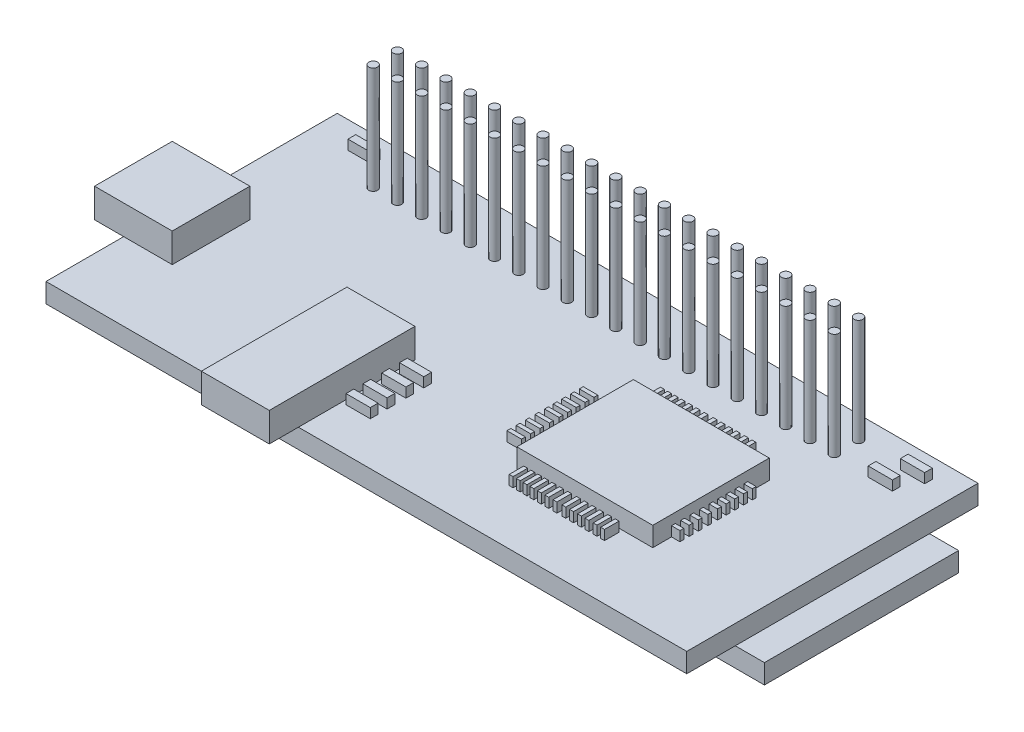
SolidWorks part; units mm, degrees
ref_plane "Front Plane" through (0, 0, 0) normal (0, 0, 1) x (1, 0, 0)
ref_plane "Top Plane" through (0, 0, 0) normal (0, 1, 0) x (1, 0, 0)
ref_plane "Right Plane" through (0, 0, 0) normal (1, 0, 0) x (0, 0, -1)
sketch "Sketch1" plane through (0, 0, 0) normal (0, 1, 0) x (1, 0, 0)
  line L0 (0, 0) -> (66, 0)
  line L1 (66, 0) -> (66, 30)
  line L2 (66, 30) -> (0, 30)
  line L3 (0, 30) -> (0, 0)
  dimension "D1" = 66
  dimension "D2" = 30
extrude "Boss-Extrude1" add sketch "Sketch1" along normal blind 2
sketch "Sketch2" plane through (0, 2, 0) normal (0, 1, 0) x (1, 0, 0)
  line L0 (0, 30) -> (0, 0) construction
  line L1 (66, 30) -> (0, 30) construction
  circle A0 centre (8.5, 27.7) radius 0.45
  circle A1 centre (8.5, 25.2) radius 0.45
  circle A2 centre (11, 27.7) radius 0.45
  circle A3 centre (11, 25.2) radius 0.45
  circle A4 centre (13.5, 27.7) radius 0.45
  circle A5 centre (13.5, 25.2) radius 0.45
  circle A6 centre (16, 27.7) radius 0.45
  circle A7 centre (16, 25.2) radius 0.45
  circle A8 centre (18.5, 27.7) radius 0.45
  circle A9 centre (18.5, 25.2) radius 0.45
  circle A10 centre (21, 27.7) radius 0.45
  circle A11 centre (21, 25.2) radius 0.45
  circle A12 centre (23.5, 27.7) radius 0.45
  circle A13 centre (23.5, 25.2) radius 0.45
  circle A14 centre (26, 27.7) radius 0.45
  circle A15 centre (26, 25.2) radius 0.45
  circle A16 centre (28.5, 27.7) radius 0.45
  circle A17 centre (28.5, 25.2) radius 0.45
  circle A18 centre (31, 27.7) radius 0.45
  circle A19 centre (31, 25.2) radius 0.45
  circle A20 centre (33.5, 27.7) radius 0.45
  circle A21 centre (33.5, 25.2) radius 0.45
  circle A22 centre (36, 27.7) radius 0.45
  circle A23 centre (36, 25.2) radius 0.45
  circle A24 centre (38.5, 27.7) radius 0.45
  circle A25 centre (38.5, 25.2) radius 0.45
  circle A26 centre (41, 27.7) radius 0.45
  circle A27 centre (41, 25.2) radius 0.45
  circle A28 centre (43.5, 27.7) radius 0.45
  circle A29 centre (43.5, 25.2) radius 0.45
  circle A30 centre (46, 27.7) radius 0.45
  circle A31 centre (46, 25.2) radius 0.45
  circle A32 centre (48.5, 27.7) radius 0.45
  circle A33 centre (48.5, 25.2) radius 0.45
  circle A34 centre (51, 27.7) radius 0.45
  circle A35 centre (51, 25.2) radius 0.45
  circle A36 centre (53.5, 27.7) radius 0.45
  circle A37 centre (53.5, 25.2) radius 0.45
  circle A38 centre (56, 27.7) radius 0.45
  circle A39 centre (56, 25.2) radius 0.45
  dimension "D1" = 0.9
  dimension "D6" = 0.9
  dimension "D2" = 8.5
  dimension "D3" = 2.3
  dimension "D4" = 2.5
  dimension "D5" = 8.5
  dimension "D7" = 20
extrude "Boss-Extrude2" add sketch "Sketch2" along normal blind 11
sketch "Sketch3" plane through (0, 2, 0) normal (0, 1, 0) x (1, 0, 0)
  line L0 (60.8, 28) -> (63.3, 28)
  line L1 (63.3, 28) -> (63.3, 27.2)
  line L2 (63.3, 27.2) -> (60.8, 27.2)
  line L3 (60.8, 27.2) -> (60.8, 28)
  line L4 (66, 30) -> (0, 30) construction
  line L5 (66, 0) -> (66, 30) construction
  line L6 (62.3, 24.8879) -> (59.8, 24.8879)
  line L7 (62.3, 25.6879) -> (62.3, 24.8879)
  line L8 (59.8, 25.6879) -> (62.3, 25.6879)
  line L9 (59.8, 24.8879) -> (59.8, 25.6879)
  line L10 (6.3546, 27.25) -> (3.8546, 27.25)
  line L11 (6.3546, 28.05) -> (6.3546, 27.25)
  line L12 (3.8546, 28.05) -> (6.3546, 28.05)
  line L13 (3.8546, 27.25) -> (3.8546, 28.05)
  line L14 (26.45, 9.9597) -> (26.45, 10.7597)
  line L15 (28.95, 10.7597) -> (28.95, 9.9597)
  line L16 (26.45, 10.7597) -> (28.95, 10.7597)
  line L17 (28.95, 9.9597) -> (26.45, 9.9597)
  line L18 (26.45, 8.1238) -> (26.45, 8.9238)
  line L19 (28.95, 8.9238) -> (28.95, 8.1238)
  line L20 (26.45, 8.9238) -> (28.95, 8.9238)
  line L21 (28.95, 8.1238) -> (26.45, 8.1238)
  line L22 (26.45, 6.186) -> (26.45, 6.986)
  line L23 (28.95, 6.986) -> (28.95, 6.186)
  line L24 (26.45, 6.986) -> (28.95, 6.986)
  line L25 (28.95, 6.186) -> (26.45, 6.186)
  line L26 (26.45, 4.4521) -> (26.45, 5.2521)
  line L27 (28.95, 5.2521) -> (28.95, 4.4521)
  line L28 (26.45, 5.2521) -> (28.95, 5.2521)
  line L29 (28.95, 4.4521) -> (26.45, 4.4521)
  dimension "D1" = 0.8
  dimension "D2" = 2.5
  dimension "D3" = 2
  dimension "D4" = 2.7
extrude "Boss-Extrude3" add sketch "Sketch3" along normal blind 1
sketch "Sketch4" plane through (0, 2, 0) normal (0, 1, 0) x (1, 0, 0)
  line L0 (26, 12) -> (26, -3)
  line L2 (26, 12) -> (19, 12)
  line L3 (19, 12) -> (19, -3)
  line L4 (26, -3) -> (19, -3)
  line L6 (0, 30) -> (0, 0) construction
  line L7 (0, 0) -> (66, 0) construction
  dimension "D1" = 19
  dimension "D2" = 7
  dimension "D3" = 3
  dimension "D4" = 15
extrude "Boss-Extrude4" add sketch "Sketch4" along normal blind 3
sketch "Sketch6" plane through (0, 2, 0) normal (0, 1, 0) x (1, 0, 0)
  line L0 (-3, 16) -> (-3, 8)
  line L2 (-3, 8) -> (5, 8)
  line L3 (5, 8) -> (5, 16)
  line L4 (5, 16) -> (-3, 16)
  line L6 (0, 30) -> (0, 0) construction
  line L7 (0, 0) -> (19, 0) construction
  dimension "D1" = 3
  dimension "D2" = 8
  dimension "D3" = 8
  dimension "D4" = 8
extrude "Boss-Extrude6" add sketch "Sketch6" along normal blind 3
sketch "Sketch7" plane through (0, 2, 0) normal (0, 1, 0) x (1, 0, 0)
  line L0 (41, 19.5) -> (55, 19.5)
  line L1 (55, 19.5) -> (55, 7.5)
  line L2 (55, 7.5) -> (41, 7.5)
  line L3 (41, 7.5) -> (41, 19.5)
  line L4 (66, 0) -> (66, 30) construction
  line L5 (26, 0) -> (66, 0) construction
  dimension "D1" = 12
  dimension "D2" = 14
  dimension "D3" = 11
  dimension "D4" = 7.5
extrude "Boss-Extrude7" add sketch "Sketch7" along normal blind 2
sketch "Sketch9" plane through (0, 2, 0) normal (0, 1, 0) x (1, 0, 0)
  line L0 (54.3702, 13.7) -> (54.3702, 13.3)
  line L1 (54.3702, 13.3) -> (55.8702, 13.3)
  line L2 (54.3702, 13.7) -> (55.8702, 13.7)
  line L3 (55.8702, 13.7) -> (55.8702, 13.3)
  line L4 (54.3702, 12.3034) -> (55.8702, 12.3034)
  line L5 (54.3702, 12.7034) -> (54.3702, 12.3034)
  line L6 (55.8702, 12.7034) -> (55.8702, 12.3034)
  line L7 (54.3702, 12.7034) -> (55.8702, 12.7034)
  line L8 (54.3702, 11.3163) -> (55.8702, 11.3163)
  line L9 (54.3702, 11.7163) -> (54.3702, 11.3163)
  line L10 (55.8702, 11.7163) -> (55.8702, 11.3163)
  line L11 (54.3702, 11.7163) -> (55.8702, 11.7163)
  line L12 (54.3702, 10.3707) -> (55.8702, 10.3707)
  line L13 (54.3702, 10.7707) -> (54.3702, 10.3707)
  line L14 (55.8702, 10.7707) -> (55.8702, 10.3707)
  line L15 (54.3702, 10.7707) -> (55.8702, 10.7707)
  line L16 (54.3702, 9.4251) -> (55.8702, 9.4251)
  line L17 (54.3702, 9.8251) -> (54.3702, 9.4251)
  line L18 (55.8702, 9.8251) -> (55.8702, 9.4251)
  line L19 (54.3702, 9.8251) -> (55.8702, 9.8251)
  line L20 (54.3702, 14.1882) -> (55.8702, 14.1882)
  line L21 (54.3702, 14.5882) -> (54.3702, 14.1882)
  line L22 (55.8702, 14.5882) -> (55.8702, 14.1882)
  line L23 (54.3702, 14.5882) -> (55.8702, 14.5882)
  line L24 (54.3702, 15.0637) -> (55.8702, 15.0637)
  line L25 (54.3702, 15.4637) -> (54.3702, 15.0637)
  line L26 (55.8702, 15.4637) -> (55.8702, 15.0637)
  line L27 (54.3702, 15.4637) -> (55.8702, 15.4637)
  line L28 (54.3702, 15.9743) -> (55.8702, 15.9743)
  line L29 (54.3702, 16.3743) -> (54.3702, 15.9743)
  line L30 (55.8702, 16.3743) -> (55.8702, 15.9743)
  line L31 (54.3702, 16.3743) -> (55.8702, 16.3743)
  line L32 (54.3702, 16.8849) -> (55.8702, 16.8849)
  line L33 (54.3702, 17.2849) -> (54.3702, 16.8849)
  line L34 (55.8702, 17.2849) -> (55.8702, 16.8849)
  line L35 (54.3702, 17.2849) -> (55.8702, 17.2849)
  line L36 (39.5528, 12.7034) -> (39.5528, 12.3034)
  line L37 (38.0528, 14.5882) -> (38.0528, 14.1882)
  line L38 (38.0528, 12.3034) -> (39.5528, 12.3034)
  line L39 (38.0528, 11.3163) -> (39.5528, 11.3163)
  line L40 (38.0528, 14.5882) -> (39.5528, 14.5882)
  line L41 (39.5528, 11.7163) -> (39.5528, 11.3163)
  line L42 (38.0528, 15.4637) -> (38.0528, 15.0637)
  line L43 (38.0528, 10.3707) -> (39.5528, 10.3707)
  line L44 (38.0528, 15.4637) -> (39.5528, 15.4637)
  line L45 (39.5528, 10.7707) -> (39.5528, 10.3707)
  line L46 (38.0528, 16.3743) -> (38.0528, 15.9743)
  line L47 (46.5835, 21.2217) -> (46.5835, 19.7217)
  line L48 (38.0528, 13.7) -> (39.5528, 13.7)
  line L49 (38.0528, 9.4251) -> (39.5528, 9.4251)
  line L50 (46.9835, 19.7217) -> (46.5835, 19.7217)
  line L51 (39.5528, 9.8251) -> (39.5528, 9.4251)
  line L52 (39.5528, 13.7) -> (39.5528, 13.3)
  line L53 (38.0528, 12.7034) -> (38.0528, 12.3034)
  line L54 (38.0528, 14.1882) -> (39.5528, 14.1882)
  line L55 (38.0528, 12.7034) -> (39.5528, 12.7034)
  line L56 (39.5528, 14.5882) -> (39.5528, 14.1882)
  line L57 (38.0528, 11.7163) -> (38.0528, 11.3163)
  line L58 (38.0528, 15.0637) -> (39.5528, 15.0637)
  line L59 (38.0528, 11.7163) -> (39.5528, 11.7163)
  line L60 (39.5528, 15.4637) -> (39.5528, 15.0637)
  line L61 (38.0528, 13.3) -> (39.5528, 13.3)
  line L62 (38.0528, 10.7707) -> (38.0528, 10.3707)
  line L63 (38.0528, 15.9743) -> (39.5528, 15.9743)
  line L64 (38.0528, 16.3743) -> (39.5528, 16.3743)
  line L65 (38.0528, 13.7) -> (38.0528, 13.3)
  line L66 (38.0528, 10.7707) -> (39.5528, 10.7707)
  line L67 (39.5528, 16.3743) -> (39.5528, 15.9743)
  line L68 (46.9835, 21.2217) -> (46.5835, 21.2217)
  line L69 (38.0528, 9.8251) -> (38.0528, 9.4251)
  line L70 (46.9835, 21.2217) -> (46.9835, 19.7217)
  line L71 (38.0528, 9.8251) -> (39.5528, 9.8251)
  line L72 (38.0528, 17.2849) -> (38.0528, 16.8849)
  line L73 (38.0528, 16.8849) -> (39.5528, 16.8849)
  line L74 (39.5528, 17.2849) -> (39.5528, 16.8849)
  line L75 (38.0528, 17.2849) -> (39.5528, 17.2849)
  line L76 (47.4941, 21.2217) -> (47.4941, 19.7217)
  line L77 (47.8941, 19.7217) -> (47.4941, 19.7217)
  line L78 (47.8941, 21.2217) -> (47.8941, 19.7217)
  line L79 (47.8941, 21.2217) -> (47.4941, 21.2217)
  line L80 (48.2996, 21.2217) -> (48.2996, 19.7217)
  line L81 (48.6996, 19.7217) -> (48.2996, 19.7217)
  line L82 (48.6996, 21.2217) -> (48.6996, 19.7217)
  line L83 (48.6996, 21.2217) -> (48.2996, 21.2217)
  line L84 (49.1051, 21.2217) -> (49.1051, 19.7217)
  line L85 (49.5051, 19.7217) -> (49.1051, 19.7217)
  line L86 (49.5051, 21.2217) -> (49.5051, 19.7217)
  line L87 (49.5051, 21.2217) -> (49.1051, 21.2217)
  line L88 (49.8756, 21.2217) -> (49.8756, 19.7217)
  line L89 (50.2756, 19.7217) -> (49.8756, 19.7217)
  line L90 (50.2756, 21.2217) -> (50.2756, 19.7217)
  line L91 (50.2756, 21.2217) -> (49.8756, 21.2217)
  line L92 (50.7162, 21.2217) -> (50.7162, 19.7217)
  line L93 (51.1162, 19.7217) -> (50.7162, 19.7217)
  line L94 (51.1162, 21.2217) -> (51.1162, 19.7217)
  line L95 (51.1162, 21.2217) -> (50.7162, 21.2217)
  line L96 (51.4866, 21.2217) -> (51.4866, 19.7217)
  line L97 (51.8866, 19.7217) -> (51.4866, 19.7217)
  line L98 (51.8866, 21.2217) -> (51.8866, 19.7217)
  line L99 (51.8866, 21.2217) -> (51.4866, 21.2217)
  line L100 (45.743, 21.2217) -> (45.743, 19.7217)
  line L101 (46.143, 19.7217) -> (45.743, 19.7217)
  line L102 (46.143, 21.2217) -> (46.143, 19.7217)
  line L103 (46.143, 21.2217) -> (45.743, 21.2217)
  line L104 (44.9725, 21.2217) -> (44.9725, 19.7217)
  line L105 (45.3725, 19.7217) -> (44.9725, 19.7217)
  line L106 (45.3725, 21.2217) -> (45.3725, 19.7217)
  line L107 (45.3725, 21.2217) -> (44.9725, 21.2217)
  line L108 (44.202, 21.2217) -> (44.202, 19.7217)
  line L109 (44.602, 19.7217) -> (44.202, 19.7217)
  line L110 (44.602, 21.2217) -> (44.602, 19.7217)
  line L111 (44.602, 21.2217) -> (44.202, 21.2217)
  line L112 (43.5016, 21.2217) -> (43.5016, 19.7217)
  line L113 (43.9016, 19.7217) -> (43.5016, 19.7217)
  line L114 (43.9016, 21.2217) -> (43.9016, 19.7217)
  line L115 (43.9016, 21.2217) -> (43.5016, 21.2217)
  line L116 (42.8011, 21.2217) -> (42.8011, 19.7217)
  line L117 (43.2011, 19.7217) -> (42.8011, 19.7217)
  line L118 (43.2011, 21.2217) -> (43.2011, 19.7217)
  line L119 (43.2011, 21.2217) -> (42.8011, 21.2217)
  line L120 (42.0656, 21.2217) -> (42.0656, 19.7217)
  line L121 (42.4656, 19.7217) -> (42.0656, 19.7217)
  line L122 (42.4656, 21.2217) -> (42.4656, 19.7217)
  line L123 (42.4656, 21.2217) -> (42.0656, 21.2217)
  line L124 (51.4866, 7.1427) -> (51.4866, 5.6427)
  line L125 (51.8866, 5.6427) -> (51.4866, 5.6427)
  line L126 (51.8866, 7.1427) -> (51.8866, 5.6427)
  line L127 (51.8866, 7.1427) -> (51.4866, 7.1427)
  line L128 (50.7162, 7.1427) -> (50.7162, 5.6427)
  line L129 (51.1162, 5.6427) -> (50.7162, 5.6427)
  line L130 (51.1162, 7.1427) -> (51.1162, 5.6427)
  line L131 (51.1162, 7.1427) -> (50.7162, 7.1427)
  line L132 (49.8756, 7.1427) -> (49.8756, 5.6427)
  line L133 (50.2756, 5.6427) -> (49.8756, 5.6427)
  line L134 (50.2756, 7.1427) -> (50.2756, 5.6427)
  line L135 (50.2756, 7.1427) -> (49.8756, 7.1427)
  line L136 (49.1051, 7.1427) -> (49.1051, 5.6427)
  line L137 (49.5051, 5.6427) -> (49.1051, 5.6427)
  line L138 (49.5051, 7.1427) -> (49.5051, 5.6427)
  line L139 (49.5051, 7.1427) -> (49.1051, 7.1427)
  line L140 (48.2996, 7.1427) -> (48.2996, 5.6427)
  line L141 (48.6996, 5.6427) -> (48.2996, 5.6427)
  line L142 (48.6996, 7.1427) -> (48.6996, 5.6427)
  line L143 (48.6996, 7.1427) -> (48.2996, 7.1427)
  line L144 (47.4941, 7.1427) -> (47.4941, 5.6427)
  line L145 (47.8941, 5.6427) -> (47.4941, 5.6427)
  line L146 (47.8941, 7.1427) -> (47.8941, 5.6427)
  line L147 (47.8941, 7.1427) -> (47.4941, 7.1427)
  line L148 (46.5835, 7.1427) -> (46.5835, 5.6427)
  line L149 (46.9835, 5.6427) -> (46.5835, 5.6427)
  line L150 (46.9835, 7.1427) -> (46.9835, 5.6427)
  line L151 (46.9835, 7.1427) -> (46.5835, 7.1427)
  line L152 (45.743, 7.1427) -> (45.743, 5.6427)
  line L153 (46.143, 5.6427) -> (45.743, 5.6427)
  line L154 (46.143, 7.1427) -> (46.143, 5.6427)
  line L155 (46.143, 7.1427) -> (45.743, 7.1427)
  line L156 (44.9725, 7.1427) -> (44.9725, 5.6427)
  line L157 (45.3725, 5.6427) -> (44.9725, 5.6427)
  line L158 (45.3725, 7.1427) -> (45.3725, 5.6427)
  line L159 (45.3725, 7.1427) -> (44.9725, 7.1427)
  line L160 (44.202, 7.1427) -> (44.202, 5.6427)
  line L161 (44.602, 5.6427) -> (44.202, 5.6427)
  line L162 (44.602, 7.1427) -> (44.602, 5.6427)
  line L163 (44.602, 7.1427) -> (44.202, 7.1427)
  line L164 (43.5016, 7.1427) -> (43.5016, 5.6427)
  line L165 (43.9016, 5.6427) -> (43.5016, 5.6427)
  line L166 (43.9016, 7.1427) -> (43.9016, 5.6427)
  line L167 (43.9016, 7.1427) -> (43.5016, 7.1427)
  line L168 (42.8011, 7.1427) -> (42.8011, 5.6427)
  line L169 (43.2011, 5.6427) -> (42.8011, 5.6427)
  line L170 (43.2011, 7.1427) -> (43.2011, 5.6427)
  line L171 (43.2011, 7.1427) -> (42.8011, 7.1427)
  line L172 (42.0656, 7.1427) -> (42.0656, 5.6427)
  line L173 (42.4656, 5.6427) -> (42.0656, 5.6427)
  line L174 (42.4656, 7.1427) -> (42.4656, 5.6427)
  line L175 (42.4656, 7.1427) -> (42.0656, 7.1427)
  dimension "D1" = 1.5
  dimension "D2" = 1.5
  dimension "D3" = 1.5
  dimension "D4" = 1.5
extrude "Boss-Extrude8" add sketch "Sketch9" along normal blind 1
sketch "Sketch10" plane through (0, 0, 0) normal (0, -1, 0) x (1, 0, 0)
  line L0 (69, -25) -> (63, -25)
  line L1 (63, -25) -> (63, -5)
  line L2 (63, -5) -> (69, -5)
  line L3 (69, -5) -> (69, -25)
  line L4 (66, -30) -> (0, -30) construction
  line L5 (66, 0) -> (66, -30) construction
  dimension "D1" = 5
  dimension "D2" = 20
  dimension "D3" = 6
  dimension "D4" = 3
extrude "Boss-Extrude9" add sketch "Sketch10" along normal blind 2
sketch "Sketch11" plane through (0, 0, 0) normal (0, -1, 0) x (1, 0, 0)
  line L0 (58, -30) -> (58, -23.5)
  line L1 (66, -30) -> (0, -30) construction
  line L2 (58, -23.5) -> (7, -23.5)
  line L3 (7, -23.5) -> (7, -30)
  line L4 (7, -30) -> (58, -30)
  line L5 (0, -30) -> (0, 0) construction
  dimension "D1" = 7
  dimension "D2" = 51
  dimension "D3" = 6.5
extrude "Boss-Extrude10" add sketch "Sketch11" along normal blind 11
